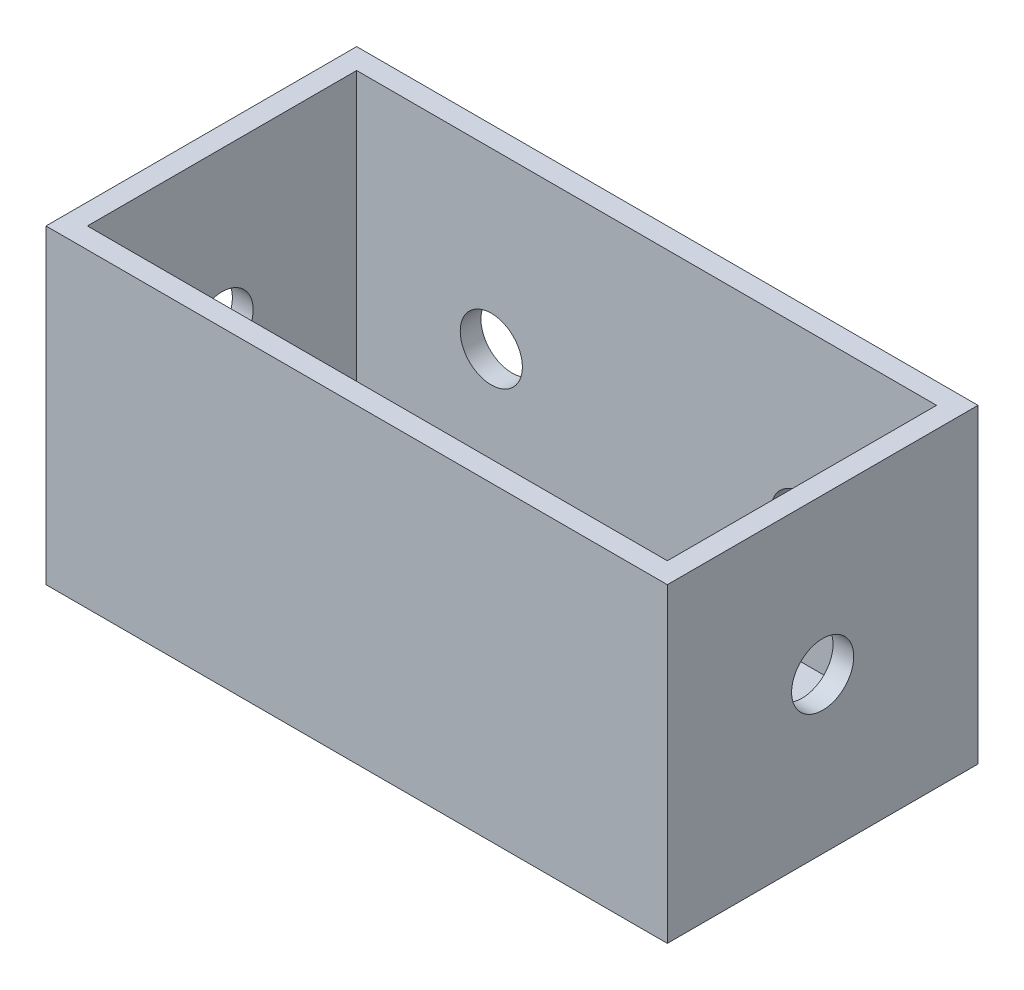
SolidWorks part; units mm, degrees
ref_plane "Front Plane" through (0, 0, 0) normal (0, 0, 1) x (1, 0, 0)
ref_plane "Top Plane" through (0, 0, 0) normal (0, 1, 0) x (1, 0, 0)
ref_plane "Right Plane" through (0, 0, 0) normal (1, 0, 0) x (0, 0, -1)
sketch "Sketch1" plane through (0, 0, 0) normal (0, 1, 0) x (1, 0, 0)
  line L1 (-15, -7.5) -> (15, -7.5)
  line L2 (-15, -7.5) -> (-15, 7.5)
  line L3 (-15, 7.5) -> (15, 7.5)
  line L4 (15, -7.5) -> (15, 7.5)
  line L5 (-15, -7.5) -> (15, 7.5) construction
  line L6 (-15, 7.5) -> (15, -7.5) construction
  point P0 (0, 0)
  dimension "D1" = 30
  dimension "D2" = 15
extrude "Boss-Extrude1" add sketch "Sketch1" along normal blind 15
sketch "Sketch2" plane through (0, 15, 0) normal (0, 1, 0) x (1, 0, 0)
  line L0 (0, 6.5) -> (0, 7.5) construction
  line L1 (-14, -6.5) -> (14, -6.5)
  line L2 (-14, -6.5) -> (-14, 6.5)
  line L3 (-14, 6.5) -> (14, 6.5)
  line L4 (14, -6.5) -> (14, 6.5)
  line L5 (-14, -6.5) -> (14, 6.5) construction
  line L6 (-14, 6.5) -> (14, -6.5) construction
  line L7 (15, 7.5) -> (-15, 7.5) construction
  line L8 (-14, 0) -> (-15, 0) construction
  line L9 (-15, 7.5) -> (-15, -7.5) construction
  point P0 (0, 0)
  dimension "D1" = 28
  dimension "D2" = 13
extrude "Cut-Extrude1" cut sketch "Sketch2" against normal blind 14
sketch "Sketch3" plane through (15, 0, 0) normal (1, 0, 0) x (0, 0, -1)
  line L0 (0, 15) -> (0, 0) construction
  line L1 (-7.5, 15) -> (7.5, 15) construction
  circle A0 centre (0, 7.5) radius 1.5
  dimension "D1" = 3
extrude "Cut-Extrude2" cut sketch "Sketch3" against normal through all
sketch "Sketch4" plane through (0, 0, -7.5) normal (0, 0, -1) x (-1, 0, 0)
  line L0 (-15, 7.5) -> (15, 3.9049) construction
  line L1 (-15, 15) -> (-15, 0) construction
  line L2 (15, 15) -> (15, 0) construction
  line L3 (0, 5.7024) -> (0, 15) construction
  line L4 (-15, 15) -> (15, 15) construction
  circle A0 centre (-7.5, 6.6012) radius 1.5
  circle A1 centre (7.5, 6.6012) radius 1.5
  dimension "D3" = 3
  dimension "D1" = 15
extrude "Cut-Extrude3" cut sketch "Sketch4" along direction (0, 0, 1) on the side against the normal up to surface (1 mm away)
